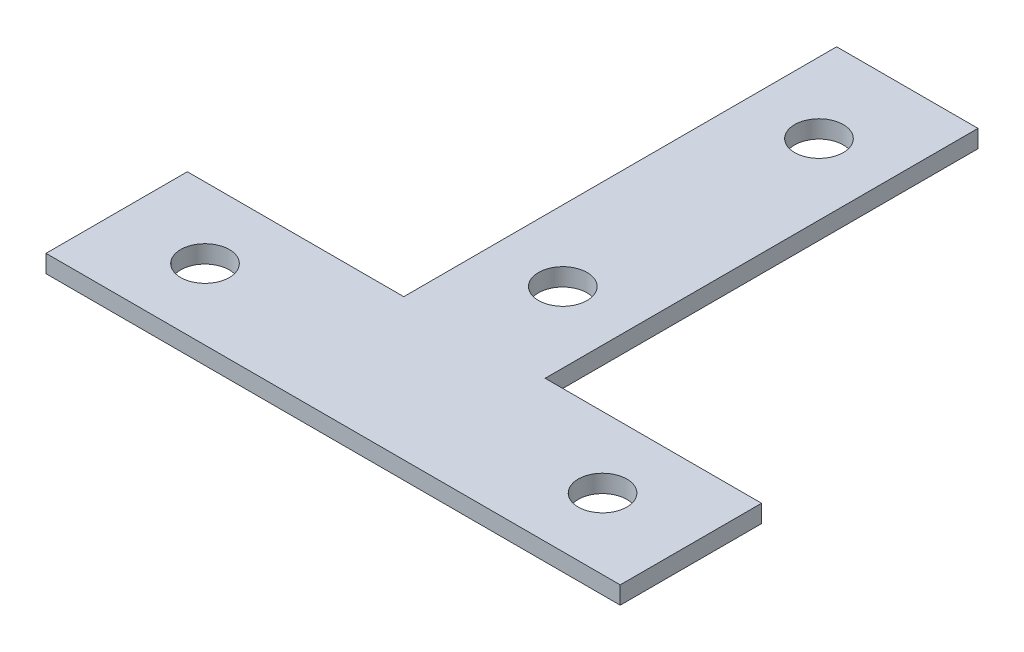
SolidWorks part; units mm, degrees
ref_plane "前视基准面" through (0, 0, 0) normal (0, 0, 1) x (1, 0, 0)
ref_plane "上视基准面" through (0, 0, 0) normal (0, 1, 0) x (1, 0, 0)
ref_plane "右视基准面" through (0, 0, 0) normal (1, 0, 0) x (0, 0, -1)
sketch "草图1" plane through (0, 0, 0) normal (0, 1, 0) x (1, 0, 0)
  line L0 (0, 0) -> (65, 0)
  line L1 (65, 0) -> (65, 16)
  line L2 (65, 16) -> (40.5, 16)
  line L3 (40.5, 16) -> (40.5, 65)
  line L4 (40.5, 65) -> (24.5, 65)
  line L5 (24.5, 65) -> (24.5, 16)
  line L6 (24.5, 16) -> (0, 16)
  line L7 (0, 16) -> (0, 0)
  line L8 (-69.0337, 8) -> (129.0787, 8) construction
  line L9 (32.5, 109.1236) -> (32.5, -39.7303) construction
  circle A0 centre (10, 8) radius 2.75
  circle A1 centre (55, 8) radius 2.75
  circle A2 centre (32.5, 55) radius 2.75
  circle A3 centre (32.5, 26) radius 2.75
  dimension "D9" = 5.5
  dimension "D10" = 5.5
  dimension "D11" = 5.5
  dimension "D12" = 5.5
  dimension "D1" = 16
  dimension "D2" = 16
  dimension "D3" = 16
  dimension "D4" = 65
  dimension "D5" = 24.5
  dimension "D6" = 49
  dimension "D7" = 8
  dimension "D8" = 8
  dimension "D13" = 45
  dimension "D14" = 10
  dimension "D15" = 29
  dimension "D16" = 10
extrude "凸台-拉伸1" add sketch "草图1" along normal blind 2
